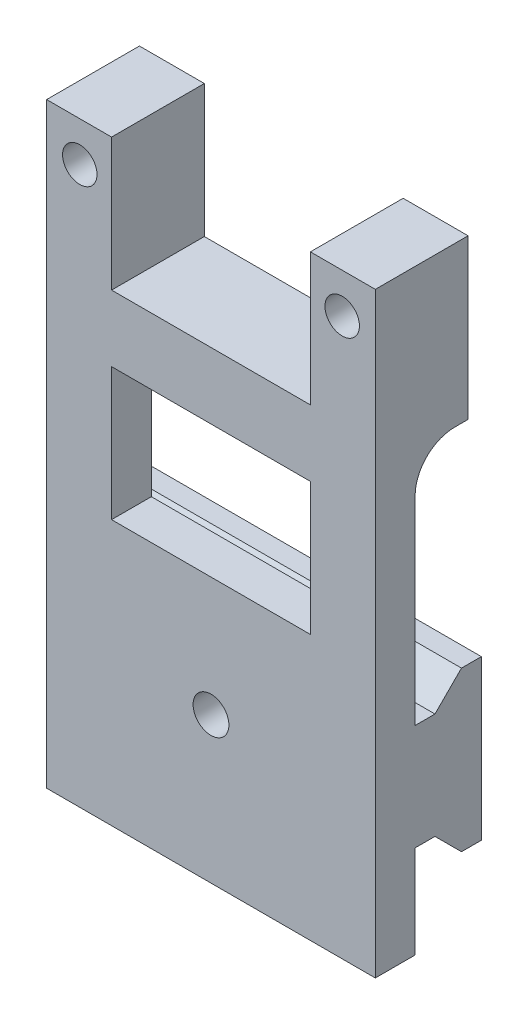
SolidWorks part; units mm, degrees
ref_plane "Front Plane" through (0, 0, 0) normal (0, 0, 1) x (1, 0, 0)
ref_plane "Top Plane" through (0, 0, 0) normal (0, 1, 0) x (1, 0, 0)
ref_plane "Right Plane" through (0, 0, 0) normal (1, 0, 0) x (0, 0, -1)
sketch "Sketch1" plane through (0, 0, 0) normal (0, 0, 1) x (1, 0, 0)
  line L0 (-7.5, 10) -> (-7.5, 0)
  line L1 (-7.5, 0) -> (7.5, 0)
  line L2 (7.5, 0) -> (7.5, 10)
  line L3 (7.5, 10) -> (12.4, 10)
  line L4 (12.4, 10) -> (12.4, -35)
  line L5 (12.4, -35) -> (-12.4, -35)
  line L6 (-12.4, -35) -> (-12.4, 10)
  line L7 (-12.4, 10) -> (-7.5, 10)
  line L8 (-9.9, 7) -> (9.9, 7) construction
  circle A0 centre (-9.9, 7) radius 1.3
  circle A1 centre (9.9, 7) radius 1.3
  point P18 (0, 0)
  point P19 (0, 7)
  dimension "D11" = 2.6
  dimension "D4" = 19.8
  dimension "D5" = 15
  dimension "D6" = 24.8
  dimension "D7" = 7
  dimension "D8" = 10
  dimension "D9" = 35
extrude "Main" add sketch "Sketch1" along normal blind 7
sketch "Sketch3" plane through (-12.4, 0, 0) normal (-1, 0, 0) x (0, 0, 1)
  line L0 (7, 10) -> (0, 10) construction
  line L1 (0, -35) -> (4, -35)
  line L2 (0, -35) -> (0, -2)
  line L3 (0, -2) -> (4, -2)
  line L4 (4, -35) -> (4, -2)
  line L5 (0, 10) -> (0, -35) construction
  line L6 (7, -35) -> (0, -35) construction
  line L7 (7, 10) -> (7, -35) construction
  point P6 (0, -50)
  point P9 (0, -35)
  dimension "D1" = 12
  dimension "D2" = 3
extrude "Cut-Extrude1" cut sketch "Sketch3" against normal through all
sketch "Sketch2" plane through (0, 0, 0) normal (-1, 0, 0) x (0, 0, 1)
  line L0 (0.5, -18) -> (-1, -18)
  line L1 (-1, -18) -> (-1, -30)
  line L2 (-1, -30) -> (0.5, -30)
  line L3 (0.5, -30) -> (2.5, -28)
  line L4 (2.5, -28) -> (4, -28)
  line L5 (4, -28) -> (4, -20)
  line L6 (4, -20) -> (2.5, -20)
  line L7 (2.5, -20) -> (0.5, -18)
  line L11 (7, -35) -> (4, -35) construction
  line L12 (4, -35) -> (4, -2) construction
  point P2 (-17.7715, -32.9443)
  point P9 (0, 0)
  point P10 (0, -28.9237)
  point P11 (3, -42)
  point P13 (-5, -44.8621)
  point P15 (-1, -46.1641)
  dimension "D1" = 5
  dimension "D2" = 8
  dimension "D3" = 1.5
  dimension "D4" = 1.5
  dimension "D5" = 135
  dimension "D6" = 12
  dimension "D7" = 5
extrude "FixSupport" add sketch "Sketch2" along normal mid plane 24.8
fillet "Fillet1" radius 3 1 edges at (0, -2, 4)
sketch "Sketch4" plane through (0, 0, 7) normal (0, 0, 1) x (1, 0, 0)
  line L1 (-7.5, -5) -> (7.5, -5)
  line L2 (-7.5, -5) -> (-7.5, -15)
  line L3 (-7.5, -15) -> (7.5, -15)
  line L4 (7.5, -5) -> (7.5, -15)
  line L5 (-7.5, 0) -> (-7.5, 10) construction
  line L6 (7.5, 10) -> (7.5, 0) construction
  line L7 (7.5, 0) -> (-7.5, 0) construction
  dimension "D1" = 5
  dimension "D2" = 10
extrude "CutForScrewRailAccess" cut sketch "Sketch4" against normal through all
sketch "Sketch5" plane through (0, 0, 7) normal (0, 0, 1) x (1, 0, 0)
  line L0 (-12.4, -18) -> (-12.4, -30) construction
  line L2 (0, -3.85) -> (0, 3.85) construction
  circle A0 centre (0, -24) radius 1.35
  point P2 (-12.4, -24)
  point P3 (-15.4798, -29.1249)
  point P6 (0, 0)
  point P7 (0, 0)
  point P10 (0, 0)
  dimension "D1" = 2.7
extrude "HoleToBlockSystemWithScrew" cut sketch "Sketch5" against normal through all
